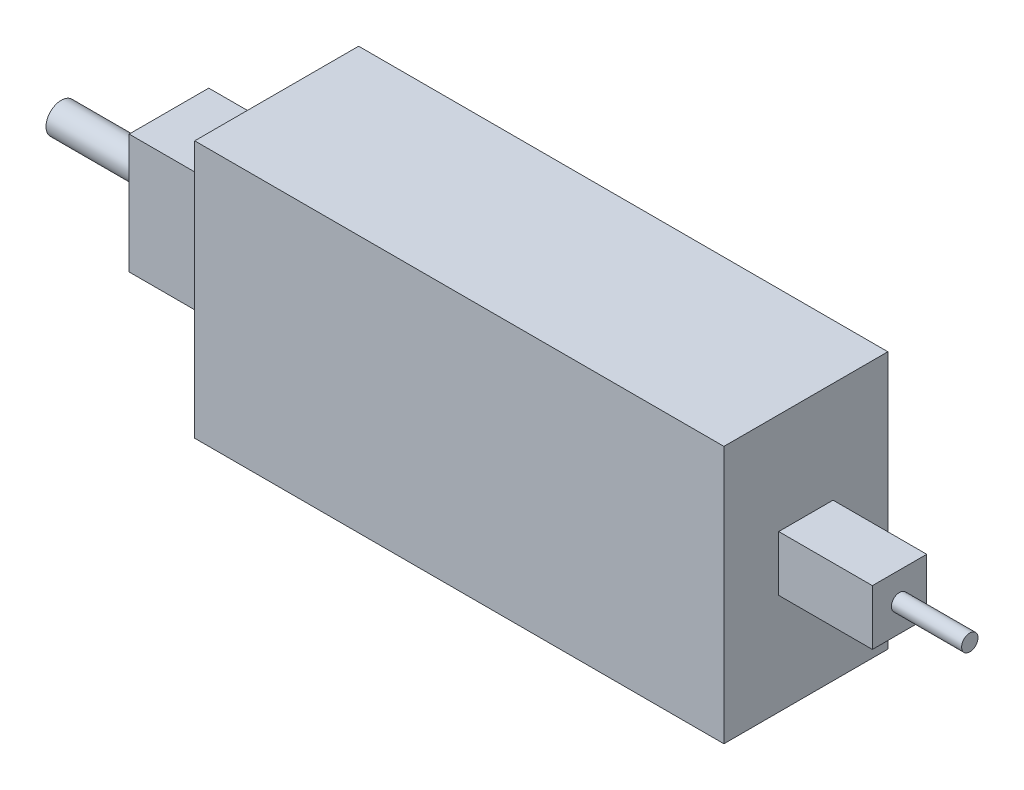
SolidWorks part; units mm, degrees
ref_plane "Front Plane" through (0, 0, 0) normal (0, 0, 1) x (1, 0, 0)
ref_plane "Top Plane" through (0, 0, 0) normal (0, 1, 0) x (1, 0, 0)
ref_plane "Right Plane" through (0, 0, 0) normal (1, 0, 0) x (0, 0, -1)
sketch "Sketch1" plane through (0, 0, 0) normal (0, 0, 1) x (1, 0, 0)
  line L0 (-295.8261, 0) -> (390.5534, 0) construction
  line L1 (0, -271.3636) -> (0, 570.3327) construction
  line L7 (0, 0) -> (113, 0)
  line L8 (0, 0) -> (0, 55)
  line L9 (0, 55) -> (113, 55)
  line L10 (113, 0) -> (113, 55)
  dimension "D1" = 113
  dimension "D2" = 55
extrude "Boss-Extrude2" add sketch "Sketch1" along normal blind 35
sketch "Sketch3" plane through (113, 0, 0) normal (1, 0, 0) x (0, 0, -1)
  line L0 (-35, 0) -> (0, 0) construction
  line L5 (-23.3, 33.4) -> (-11.7, 33.4)
  line L6 (-23.3, 33.4) -> (-23.3, 21.6)
  line L7 (-23.3, 21.6) -> (-11.7, 21.6)
  line L8 (-11.7, 33.4) -> (-11.7, 21.6)
  line L9 (0, 0) -> (0, 55) construction
  dimension "D1" = 11.6
  dimension "D2" = 11.8
  dimension "D3" = 21.6
  dimension "D4" = 11.7
extrude "Boss-Extrude3" add sketch "Sketch3" along normal blind 20
sketch "Sketch4" plane through (133, 0, 0) normal (1, 0, 0) x (0, 0, -1)
  line L0 (-23.3, 21.6) -> (-11.7, 21.6) construction
  line L1 (-23.3, 33.4) -> (-23.3, 21.6) construction
  circle A0 centre (-17.5, 27.5) radius 1.75
  point P4 (0, 0)
  dimension "D1" = 3.5
  dimension "D2" = 5.9
  dimension "D3" = 5.8
extrude "Boss-Extrude4" add sketch "Sketch4" along normal blind 15
sketch "Sketch5" plane through (0, 0, 0) normal (-1, 0, 0) x (0, 0, 1)
  line L0 (35, 0) -> (0, 0) construction
  line L1 (9, 40.25) -> (26, 40.25)
  line L2 (9, 40.25) -> (9, 14.75)
  line L3 (9, 14.75) -> (26, 14.75)
  line L4 (26, 40.25) -> (26, 14.75)
  line L5 (35, 55) -> (35, 0) construction
  dimension "D1" = 25.5
  dimension "D2" = 17
  dimension "D3" = 14.75
  dimension "D4" = 9
extrude "Boss-Extrude5" add sketch "Sketch5" along normal blind 23
sketch "Sketch6" plane through (-23, 0, 0) normal (-1, 0, 0) x (0, 0, 1)
  line L0 (26, 14.75) -> (26, 40.25) construction
  line L1 (26, 40.25) -> (9, 40.25) construction
  circle A0 centre (17.5, 27.5) radius 3.25
  dimension "D1" = 6.5
  dimension "D2" = 8.5
  dimension "D3" = 12.75
extrude "Boss-Extrude6" add sketch "Sketch6" along normal blind 23
